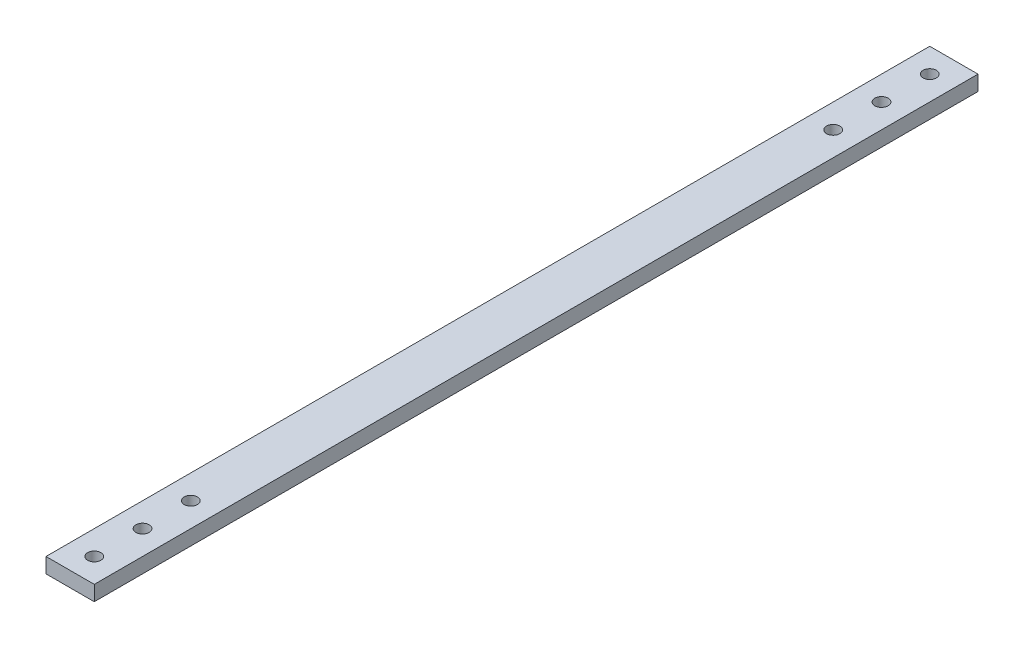
SolidWorks part; units mm, degrees
ref_plane "Front Plane" through (0, 0, 0) normal (0, 0, 1) x (1, 0, 0)
ref_plane "Top Plane" through (0, 0, 0) normal (0, 1, 0) x (1, 0, 0)
ref_plane "Right Plane" through (0, 0, 0) normal (1, 0, 0) x (0, 0, -1)
sketch "Sketch1" plane through (0, 0, 0) normal (0, 0, 1) x (1, 0, 0)
  line L0 (0, 3.9688) -> (0, -3.9688)
  line L1 (-12.7, 0) -> (12.7, 0) construction
  point P6 (0, 0)
  dimension "Width" = 25.4
  dimension "Thk" = 7.9375
sketch "Sketch2" plane through (0, 0, 0) normal (1, 0, 0) x (0, 0, -1)
  line L0 (152.4, 0) -> (-152.4, 0)
  point P4 (0, 0)
  dimension "Length" = 304.8
sketch "Sketch3" plane through (0, 0, 0) normal (0, 0, 1) x (1, 0, 0)
  line L1 (12.7, 3.9688) -> (-12.7, 3.9688)
  line L2 (12.7, 3.9688) -> (12.7, -3.9688)
  line L3 (12.7, -3.9688) -> (-12.7, -3.9688)
  line L4 (-12.7, 3.9688) -> (-12.7, -3.9688)
  line L5 (12.7, 3.9688) -> (-12.7, -3.9688) construction
  line L6 (12.7, -3.9688) -> (-12.7, 3.9688) construction
  point P0 (0, 0)
extrude "Boss-Extrude1" add sketch "Sketch3" along normal mid plane 465
sketch "Sketch4" plane through (0, 3.9688, 0) normal (0, 1, 0) x (1, 0, 0)
  line L0 (0, 0) -> (237.3498, 0) construction
  line L1 (12.7, 232.5) -> (-12.7, 232.5) construction
  line L2 (12.7, -232.5) -> (12.7, 232.5) construction
  circle A0 centre (0, 219.8) radius 3.5
  circle A1 centre (0, 194.4) radius 3.5
  circle A2 centre (0, 169) radius 3.5
  circle A3 centre (0, -169) radius 3.5
  circle A4 centre (0, -194.4) radius 3.5
  circle A5 centre (0, -219.8) radius 3.5
  point P11 (0, 232.5)
  point P14 (0, 0)
  dimension "D1" = 12.7
  dimension "D2" = 25.4
  dimension "D3" = 7
  dimension "D4" = 7
  dimension "D5" = 7
  dimension "D6" = 25.4
  dimension "D7" = 12.7
extrude "Cut-Extrude1" cut sketch "Sketch4" against normal through all
